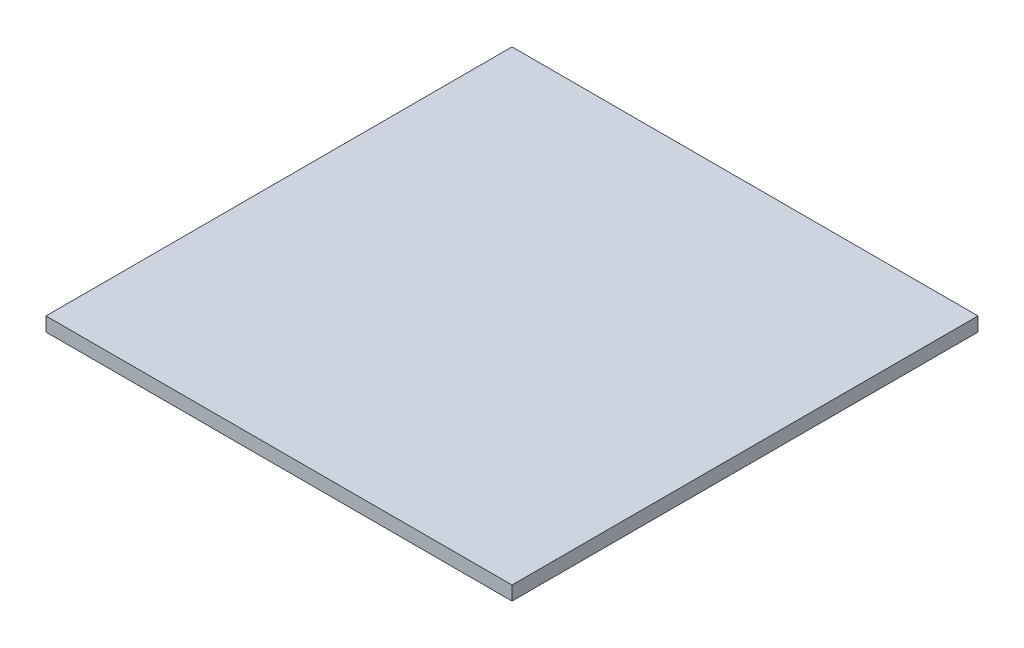
SolidWorks part; units mm, degrees
ref_plane "Front Plane" through (0, 0, 0) normal (0, 0, 1) x (1, 0, 0)
ref_plane "Top Plane" through (0, 0, 0) normal (0, 1, 0) x (1, 0, 0)
ref_plane "Right Plane" through (0, 0, 0) normal (1, 0, 0) x (0, 0, -1)
sketch "Sketch1" plane through (0, 0, 0) normal (0, 1, 0) x (1, 0, 0)
  line L1 (50, -50) -> (-50, -50)
  line L2 (50, -50) -> (50, 50)
  line L3 (50, 50) -> (-50, 50)
  line L4 (-50, -50) -> (-50, 50)
  line L5 (50, -50) -> (-50, 50) construction
  line L6 (50, 50) -> (-50, -50) construction
  point P0 (0, 0)
  dimension "D1" = 100
  dimension "D2" = 100
extrude "Boss-Extrude1" add sketch "Sketch1" along normal blind 3
sketch "Sketch2" plane through (0, 3, 0) normal (0, 1, 0) x (1, 0, 0)
  line L0 (-50, -50) -> (50, -50) construction
  line L1 (-50, 50) -> (-50, -50) construction
  line L2 (-25, -38.4) -> (-25, 0) construction
  line L3 (-23.4, 0) -> (-25, 0) construction
  circle A0 centre (-23.4, 0) radius 1.6
  circle A1 centre (21.468, 0) radius 1.6
  circle A2 centre (27.5469, -27.1872) radius 1.6
  circle A3 centre (-25, -40) radius 1.6
  point P14 (0, 0)
  dimension "D1" = 3.2
  dimension "D2" = 3.2
  dimension "D3" = 3.2
  dimension "D4" = 10
  dimension "D5" = 25
  dimension "D6" = 38.4
  dimension "D7" = 38.4
